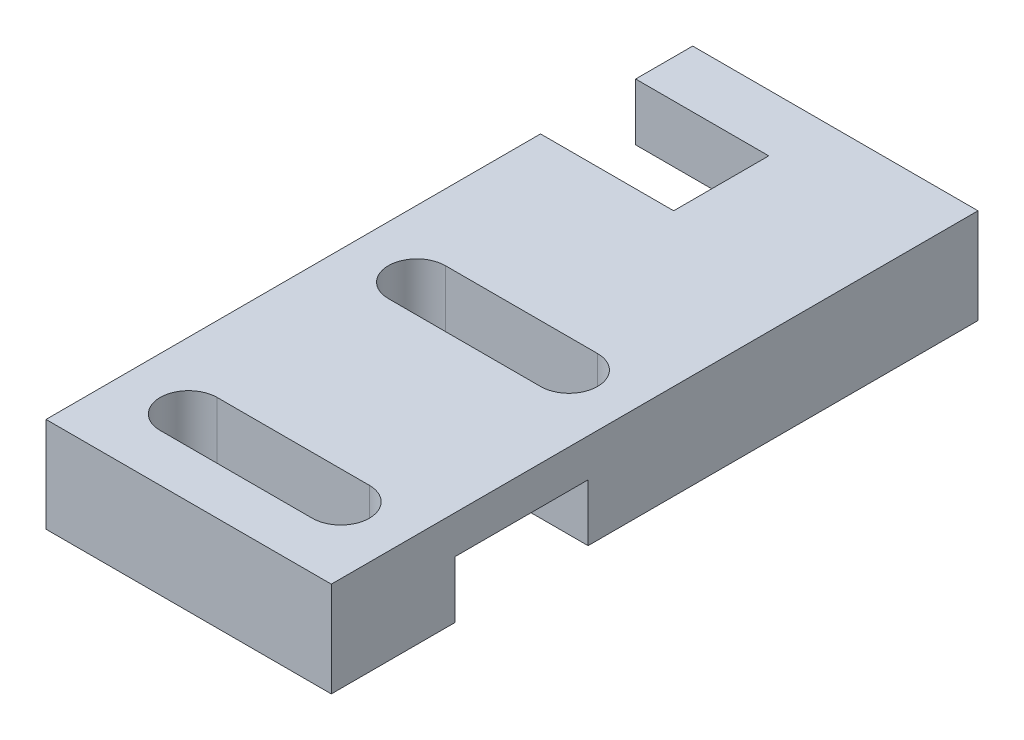
SolidWorks part; units mm, degrees
ref_plane "前视基准面" through (0, 0, 0) normal (0, 0, 1) x (1, 0, 0)
ref_plane "上视基准面" through (0, 0, 0) normal (0, 1, 0) x (1, 0, 0)
ref_plane "右视基准面" through (0, 0, 0) normal (1, 0, 0) x (0, 0, -1)
sketch "草图1" plane through (0, 0, 0) normal (0, 1, 0) x (1, 0, 0)
  line L0 (0, 34) -> (15, 34)
  line L1 (0, -55) -> (0, 55) construction
  line L2 (15, 34) -> (15, 0)
  line L3 (-55, 0) -> (55, 0) construction
  line L4 (15, 0) -> (0, 0)
  line L5 (0, 0) -> (0, 34)
  line L6 (3.5, 4) -> (11.5, 4) construction
  line L7 (3.5, 5.5) -> (11.5, 5.5)
  line L8 (3.5, 2.5) -> (11.5, 2.5)
  line L9 (0, 31) -> (7, 31)
  line L10 (3.5, 16) -> (11.5, 16) construction
  line L11 (3.5, 17.5) -> (11.5, 17.5)
  line L12 (3.5, 14.5) -> (11.5, 14.5)
  line L13 (7, 31) -> (7, 26)
  line L14 (7, 26) -> (0, 26)
  arc A0 (3.5, 5.5) -> (3.5, 2.5) centre (3.5, 4) ccw
  arc A1 (11.5, 2.5) -> (11.5, 5.5) centre (11.5, 4) ccw
  arc A2 (3.5, 17.5) -> (3.5, 14.5) centre (3.5, 16) ccw
  arc A3 (11.5, 14.5) -> (11.5, 17.5) centre (11.5, 16) ccw
  point P11 (7.5, 4)
  point P20 (7.5, 16)
  dimension "D3" = 1.5
  dimension "D6" = 1.5
  dimension "D1" = 34
  dimension "D2" = 15
  dimension "D4" = 8
  dimension "D5" = 8
  dimension "D7" = 7.5
  dimension "D8" = 7.5
  dimension "D9" = 4
  dimension "D10" = 3
  dimension "D11" = 12
  dimension "D12" = 5
  dimension "D13" = 8
extrude "凸台-拉伸1" add sketch "草图1" along normal blind 5 contours L13 L14 L5 L4 L2 L0 L9 A3 L12 A2 L11 A1 L8 A0 L7
sketch "草图2" plane through (0, 0, 0) normal (-1, 0, 0) x (0, 0, 1)
  line L0 (0, -2.75) -> (0, 2.75) construction
  line L1 (-13.5, 3) -> (-6.5, 3)
  line L2 (-13.5, 3) -> (-13.5, 0)
  line L3 (-13.5, 0) -> (-6.5, 0)
  line L4 (-6.5, 3) -> (-6.5, 0)
  dimension "D1" = 3
  dimension "D2" = 7
  dimension "D3" = 6.5
extrude "切除-拉伸1" cut sketch "草图2" against normal through all
sketch "草图3" plane through (7, 0, 0) normal (-1, 0, 0) x (0, 0, 1)
  line L0 (-34, 5) -> (-34, 0) construction
  line L1 (-34, 2) -> (-31, 2)
  line L2 (-34, 2) -> (-34, 0)
  line L3 (-34, 0) -> (-31, 0)
  line L4 (-31, 2) -> (-31, 0)
  line L5 (8.25, 0) -> (-8.25, 0) construction
  line L6 (-31, 5) -> (-31, 0) construction
  dimension "D1" = 2
extrude "切除-拉伸2" cut sketch "草图3" along normal blind 12
